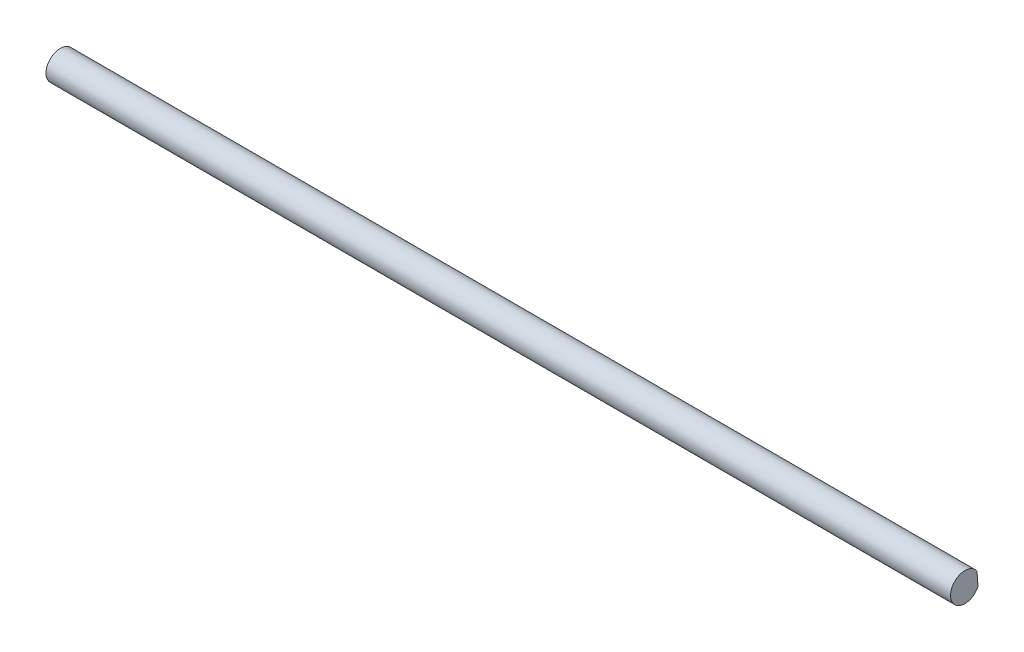
SolidWorks part; units mm, degrees
ref_plane "Plan de face" through (0, 0, 0) normal (0, 0, 1) x (1, 0, 0)
ref_plane "Plan de dessus" through (0, 0, 0) normal (0, 1, 0) x (1, 0, 0)
ref_plane "Plan de droite" through (0, 0, 0) normal (1, 0, 0) x (0, 0, -1)
sketch "Esquisse1" plane through (0, 0, 0) normal (1, 0, 0) x (0, 0, -1)
  line L1 (2.8915, -1.3114) -> (2.6832, 1.6974)
  arc A0 (2.6832, 1.6974) -> (2.8915, -1.3114) centre (0, 0) ccw
  dimension "D1" = 6.35
  dimension "D2" = 2.794
extrude "Boss.-Extru.1" add sketch "Esquisse1" along normal blind 200
